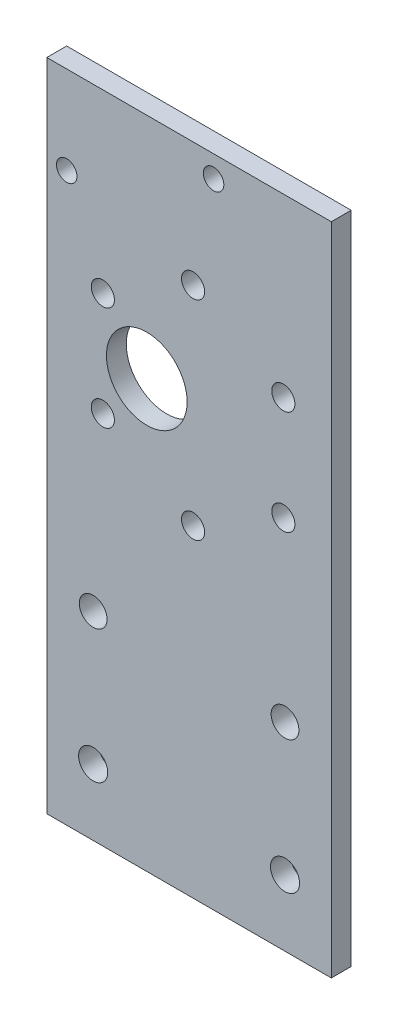
SolidWorks part; units mm, degrees
ref_plane "正面" through (0, 0, 0) normal (0, 0, 1) x (1, 0, 0)
ref_plane "平面" through (0, 0, 0) normal (0, 1, 0) x (1, 0, 0)
ref_plane "右側面" through (0, 0, 0) normal (1, 0, 0) x (0, 0, -1)
sketch "ｽｹｯﾁ1" plane through (0, 0, 0) normal (0, 0, 1) x (1, 0, 0)
  line L1 (-20, 14.5) -> (20, 14.5)
  line L2 (-20, 14.5) -> (-20, -14.5)
  line L3 (-20, -14.5) -> (20, -14.5)
  line L4 (20, 14.5) -> (20, -14.5)
  line L5 (-20, 14.5) -> (20, -14.5) construction
  line L6 (-20, -14.5) -> (20, 14.5) construction
  point P0 (0, 0)
  dimension "D1" = 40
  dimension "D2" = 29
extrude "ﾎﾞｽ - 押し出し1" add sketch "ｽｹｯﾁ1" along normal blind 3
sketch "ｽｹｯﾁ2" plane through (0, 0, 3) normal (0, 0, 1) x (1, 0, 0)
  line L1 (-20, 14.5) -> (-16.5, 14.5)
  line L2 (-20, 14.5) -> (-20, 10.5)
  line L3 (-20, 10.5) -> (-16.5, 10.5)
  line L4 (-16.5, 14.5) -> (-16.5, 10.5)
  line L5 (-20, -14.5) -> (-16.5, -14.5)
  line L6 (-20, -14.5) -> (-20, -10.5)
  line L7 (-20, -10.5) -> (-16.5, -10.5)
  line L8 (-16.5, -14.5) -> (-16.5, -10.5)
  line L9 (20, -14.5) -> (16.5, -14.5)
  line L10 (20, -14.5) -> (20, -10.5)
  line L11 (20, -10.5) -> (16.5, -10.5)
  line L12 (16.5, -14.5) -> (16.5, -10.5)
  line L13 (20, 14.5) -> (16.5, 14.5)
  line L14 (20, 14.5) -> (20, 10.5)
  line L15 (20, 10.5) -> (16.5, 10.5)
  line L16 (16.5, 14.5) -> (16.5, 10.5)
  circle A0 centre (-16.5, 10.5) radius 2.1
  circle A1 centre (-16.5, -10.5) radius 2.1
  circle A2 centre (16.5, -10.5) radius 2.1
  circle A3 centre (16.5, 10.5) radius 2.1
  dimension "D9" = 4.2
  dimension "D10" = 4.2
  dimension "D11" = 4.2
  dimension "D12" = 4.2
  dimension "D1" = 3.5
  dimension "D2" = 4
  dimension "D3" = 3.5
  dimension "D4" = 4
  dimension "D5" = 3.5
  dimension "D6" = 4
  dimension "D7" = 3.5
  dimension "D8" = 4
extrude "ｶｯﾄ - 押し出し1" cut sketch "ｽｹｯﾁ2" against normal blind 3 contours L3 A0 L4 | L4 A0 L3 | L8 A1 L7 | L7 A1 L8 | L12 A2 L11 | L11 A2 L12 | L16 A3 L15 | L15 A3 L16
sketch "ｽｹｯﾁ3" plane through (0, -14.5, 0) normal (0, -1, 0) x (1, 0, 0)
  line L1 (20, 0) -> (-20, 0)
  line L2 (20, 0) -> (20, 3)
  line L3 (20, 3) -> (-20, 3)
  line L4 (-20, 0) -> (-20, 3)
extrude "ﾎﾞｽ - 押し出し2" add sketch "ｽｹｯﾁ3" along normal blind 10
sketch "ｽｹｯﾁ4" plane through (0, 14.5, 0) normal (0, 1, 0) x (1, 0, 0)
  line L1 (20, -3) -> (-20, -3)
  line L2 (20, -3) -> (20, 0)
  line L3 (20, 0) -> (-20, 0)
  line L4 (-20, -3) -> (-20, 0)
extrude "ﾎﾞｽ - 押し出し3" add sketch "ｽｹｯﾁ4" along normal blind 10
sketch "ｽｹｯﾁ6" plane through (20, 0, 0) normal (1, 0, 0) x (0, 0, -1)
  line L1 (0, 24.5) -> (-3, 24.5)
  line L2 (0, 24.5) -> (0, -24.5)
  line L3 (0, -24.5) -> (-3, -24.5)
  line L4 (-3, 24.5) -> (-3, -24.5)
extrude "ﾎﾞｽ - 押し出し5" add sketch "ｽｹｯﾁ6" along normal blind 42
sketch "ｽｹｯﾁ7" plane through (0, 0, 3) normal (0, 0, 1) x (1, 0, 0)
  line L0 (62, 0) -> (43.1058, 0)
  line L1 (62, 24.5) -> (62, -24.5) construction
  line L2 (43.1058, 0) -> (36.1058, 0)
  line L7 (31.9689, -11.1369) -> (54.2427, 11.1369) construction
  line L8 (31.9689, 11.1369) -> (54.2427, -11.1369) construction
  line L9 (43.1058, 0) -> (29.4659, 7.875)
  line L10 (43.1058, 0) -> (43.1058, 15.75)
  line L11 (43.1058, 0) -> (56.7457, 7.875)
  line L12 (43.1058, 0) -> (29.4659, -7.875)
  line L13 (43.1058, 0) -> (43.1058, -15.75)
  line L14 (43.1058, 0) -> (56.7457, -7.875)
  circle A0 centre (43.1058, 0) radius 15.75
  circle A5 centre (29.4659, 7.875) radius 1.75
  circle A6 centre (43.1058, 15.75) radius 1.75
  circle A7 centre (29.4659, -7.875) radius 1.75
  circle A8 centre (43.1058, -15.75) radius 1.75
  circle A9 centre (56.7457, -7.875) radius 1.75
  circle A10 centre (56.7457, 7.875) radius 1.75
  circle A11 centre (36.1058, 0) radius 6.1
  dimension "D3" = 60
  dimension "D4" = 7
  dimension "D5" = 60
  dimension "D6" = 60
  dimension "D7" = 31.5
  dimension "D8" = 3.5
  dimension "D9" = 3.5
  dimension "D10" = 3.5
  dimension "D11" = 3.5
  dimension "D12" = 3.5
  dimension "D13" = 3.5
  dimension "D14" = 12.2
  dimension "D2" = 60
sketch "ｽｹｯﾁ8" plane through (-20, 0, 0) normal (-1, 0, 0) x (0, 0, 1)
  line L1 (3, -24.5) -> (0, -24.5)
  line L2 (3, -24.5) -> (3, 24.5)
  line L3 (3, 24.5) -> (0, 24.5)
  line L4 (0, -24.5) -> (0, 24.5)
extrude "ﾎﾞｽ - 押し出し6" add sketch "ｽｹｯﾁ8" along normal blind 2
sketch "ｽｹｯﾁ9" plane through (62, 0, 0) normal (1, 0, 0) x (0, 0, -1)
  line L1 (0, 24.5) -> (-3, 24.5)
  line L2 (0, 24.5) -> (0, -24.5)
  line L3 (0, -24.5) -> (-3, -24.5)
  line L4 (-3, 24.5) -> (-3, -24.5)
extrude "ﾎﾞｽ - 押し出し7" add sketch "ｽｹｯﾁ9" along normal blind 2
sketch "ｽｹｯﾁ10" plane through (0, -24.5, 0) normal (0, -1, 0) x (1, 0, 0)
  line L1 (-22, 0) -> (64, 0)
  line L2 (-22, 0) -> (-22, 3)
  line L3 (-22, 3) -> (64, 3)
  line L4 (64, 0) -> (64, 3)
extrude "ﾎﾞｽ - 押し出し8" add sketch "ｽｹｯﾁ10" along normal blind 10
sketch "ｽｹｯﾁ11" plane through (0, 24.5, 0) normal (0, 1, 0) x (1, 0, 0)
  line L1 (-22, 0) -> (64, 0)
  line L2 (-22, 0) -> (-22, -3)
  line L3 (-22, -3) -> (64, -3)
  line L4 (64, 0) -> (64, -3)
extrude "ﾎﾞｽ - 押し出し9" add sketch "ｽｹｯﾁ11" along normal blind 10
sketch "ｽｹｯﾁ12" plane through (0, 0, 3) normal (0, 0, 1) x (1, 0, 0)
  line L0 (64, -34.5) -> (64, -27)
  line L1 (64, 34.5) -> (64, -34.5) construction
  line L2 (64, 34.5) -> (64, 27)
  line L3 (64, -27) -> (54, -27)
  line L4 (64, 27) -> (54, 27)
  line L5 (-22, -34.5) -> (-22, -27)
  line L6 (-22, -34.5) -> (-22, 34.5) construction
  line L7 (-22, 34.5) -> (-22, 27)
  line L8 (-22, -27) -> (-12, -27)
  line L9 (-22, 27) -> (-12, 27)
  circle A0 centre (54, -27) radius 2.2
  circle A1 centre (54, 27) radius 2.2
  circle A2 centre (-12, -27) radius 2.2
  circle A3 centre (-12, 27) radius 2.2
  dimension "D4" = 4.4
  dimension "D5" = 4.4
  dimension "D11" = 4.4
  dimension "D12" = 4.4
  dimension "D1" = 7.5
  dimension "D2" = 7.5
  dimension "D3" = 10
  dimension "D6" = 10
  dimension "D7" = 7.5
  dimension "D8" = 7.5
  dimension "D9" = 10
  dimension "D10" = 10
extrude "ｶｯﾄ - 押し出し4" cut sketch "ｽｹｯﾁ7" against normal blind 10
sketch "ｽｹｯﾁ14" plane through (-22, 0, 0) normal (-1, 0, 0) x (0, 0, 1)
  line L0 (0, 34.5) -> (0, -34.5) construction
  line L1 (3, -34.5) -> (0, -34.5)
  line L2 (3, -34.5) -> (3, 34.5)
  line L3 (3, 34.5) -> (0, 34.5)
  line L4 (0, -34.5) -> (0, 34.5)
  line L5 (0, 34.5) -> (3, 34.5) construction
extrude "ｶｯﾄ - 押し出し5" cut sketch "ｽｹｯﾁ14" against normal blind 43
sketch "ｽｹｯﾁ17" plane through (0, -34.5, 0) normal (0, -1, 0) x (1, 0, 0)
  line L1 (21, 3) -> (64, 3)
  line L2 (21, 3) -> (21, 0)
  line L3 (21, 0) -> (64, 0)
  line L4 (64, 3) -> (64, 0)
extrude "ﾎﾞｽ - 押し出し10" add sketch "ｽｹｯﾁ17" along normal blind 20
sketch "ｽｹｯﾁ18" plane through (0, 0, 3) normal (0, 0, 1) x (1, 0, 0)
  line L0 (21, -54.5) -> (21, -34.5)
  line L1 (21, -54.5) -> (21, 34.5) construction
  line L3 (64, -54.5) -> (64, -34.5)
  line L4 (64, 34.5) -> (64, -54.5) construction
  line L5 (64, -34.5) -> (57, -34.5)
  line L6 (21, -34.5) -> (28, -34.5)
  circle A0 centre (28, -34.5) radius 2.1
  circle A1 centre (57, -34.5) radius 2.1
  dimension "D5" = 4.2
  dimension "D6" = 4.2
  dimension "D1" = 20
  dimension "D2" = 20
  dimension "D3" = 7
  dimension "D4" = 7
extrude "ｶｯﾄ - 押し出し6" cut sketch "ｽｹｯﾁ18" against normal blind 10
sketch "ｽｹｯﾁ19" plane through (0, 0, 3) normal (0, 0, 1) x (1, 0, 0)
  line L0 (42.5, -54.5) -> (42.5, 34.5)
  line L1 (64, -54.5) -> (21, -54.5) construction
  line L2 (21, 34.5) -> (64, 34.5) construction
  circle A0 centre (28, -34.5) radius 2.1 construction
  circle A1 centre (57, -34.5) radius 2.1 construction
  dimension "D2" = 14.5
  dimension "D1" = 14.5
sketch "ｽｹｯﾁ20" plane through (0, -54.5, 0) normal (0, -1, 0) x (1, 0, 0)
  line L1 (64, 0) -> (21, 0)
  line L2 (64, 0) -> (64, 3)
  line L3 (64, 3) -> (21, 3)
  line L4 (21, 0) -> (21, 3)
extrude "ﾎﾞｽ - 押し出し11" add sketch "ｽｹｯﾁ20" along normal blind 10
sketch "ｽｹｯﾁ21" plane through (0, 34.5, 0) normal (0, 1, 0) x (1, 0, 0)
  line L1 (64, 0) -> (21, 0)
  line L2 (64, 0) -> (64, -3)
  line L3 (64, -3) -> (21, -3)
  line L4 (21, 0) -> (21, -3)
extrude "ｶｯﾄ - 押し出し7" cut sketch "ｽｹｯﾁ21" against normal blind 10
sketch "ｽｹｯﾁ22" plane through (0, 0, 3) normal (0, 0, 1) x (1, 0, 0)
  line L0 (28, -34.5) -> (28, -54.5)
  line L1 (57, -34.5) -> (57, -54.5)
  circle A0 centre (28, -54.5) radius 2.2
  circle A1 centre (57, -54.5) radius 2.2
  dimension "D2" = 4.4
  dimension "D4" = 4.4
  dimension "D1" = 20
  dimension "D3" = 20
extrude "ｶｯﾄ - 押し出し8" cut sketch "ｽｹｯﾁ22" against normal blind 10
sketch "ｽｹｯﾁ23" plane through (0, 0, 3) normal (0, 0, 1) x (1, 0, 0)
  line L0 (21, 24.5) -> (21, 22.0635)
  line L1 (21, -64.5) -> (21, 24.5) construction
  line L2 (21, 22.0635) -> (24.0484, 22.0635)
  line L3 (24.0484, 22.0635) -> (24.0484, 11.7635)
  line L4 (24.0484, 11.7635) -> (46.2484, 11.7635)
  line L5 (64, 24.5) -> (21, 24.5) construction
  dimension "D1" = 10.3
  dimension "D2" = 22.2
sketch "ｽｹｯﾁ24" plane through (0, 24.5, 0) normal (0, 1, 0) x (1, 0, 0)
  line L1 (21, 0) -> (64, 0)
  line L2 (21, 0) -> (21, -3)
  line L3 (21, -3) -> (64, -3)
  line L4 (64, 0) -> (64, -3)
extrude "ﾎﾞｽ - 押し出し12" add sketch "ｽｹｯﾁ24" along normal blind 10
sketch "ｽｹｯﾁ25" plane through (0, 0, 3) normal (0, 0, 1) x (1, 0, 0)
  line L0 (21, 34.5) -> (21, 31.5)
  line L1 (21, -64.5) -> (21, 34.5) construction
  line L2 (21, 31.5) -> (24, 31.5)
  line L3 (24, 31.5) -> (24, 21.2)
  line L4 (24, 21.2) -> (46.2, 21.2)
  line L5 (46.2, 21.2) -> (46.2, 31.2)
  circle A0 centre (24, 21.2) radius 1.55
  circle A1 centre (46.2, 31.2) radius 1.55
  dimension "D6" = 3.1
  dimension "D7" = 3.1
  dimension "D1" = 3
  dimension "D2" = 3
  dimension "D3" = 10.3
  dimension "D4" = 22.2
  dimension "D5" = 10
extrude "ｶｯﾄ - 押し出し9" cut sketch "ｽｹｯﾁ25" against normal blind 10
